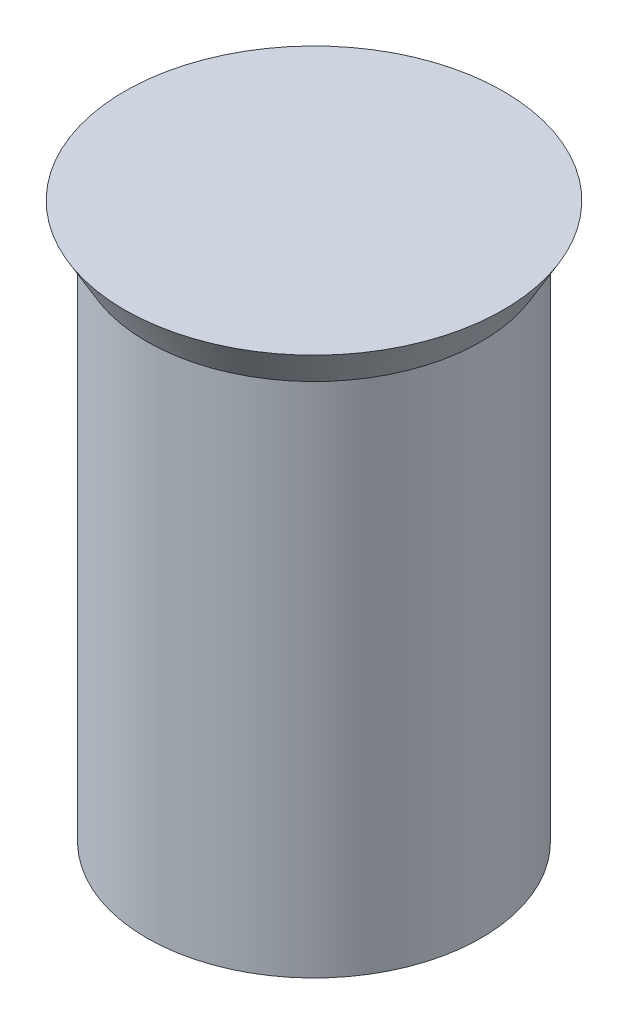
SolidWorks part; units mm, degrees
ref_plane "Front Plane" through (0, 0, 0) normal (0, 0, 1) x (1, 0, 0)
ref_plane "Top Plane" through (0, 0, 0) normal (0, 1, 0) x (1, 0, 0)
ref_plane "Right Plane" through (0, 0, 0) normal (1, 0, 0) x (0, 0, -1)
sketch "Sketch1" plane through (0, 0, 0) normal (1, 0, 0) x (0, 0, -1)
  line L0 (0, 0) -> (1.625, 0)
  line L1 (0, 0) -> (0, -4.7625) construction
  line L2 (1.625, 0) -> (1.435, -0.3302)
  line L3 (1.435, -0.3302) -> (1.435, -4.7625)
  line L4 (1.435, -4.7625) -> (0, -4.7625)
  line L5 (0, 0) -> (0, -4.7625)
  dimension "D1" = 3.25
  dimension "D2" = 0.3302
  dimension "D3" = 2.87
  dimension "D4" = 4.7625
revolve "Revolve1" add sketch "Sketch1" angle 360 about L1
